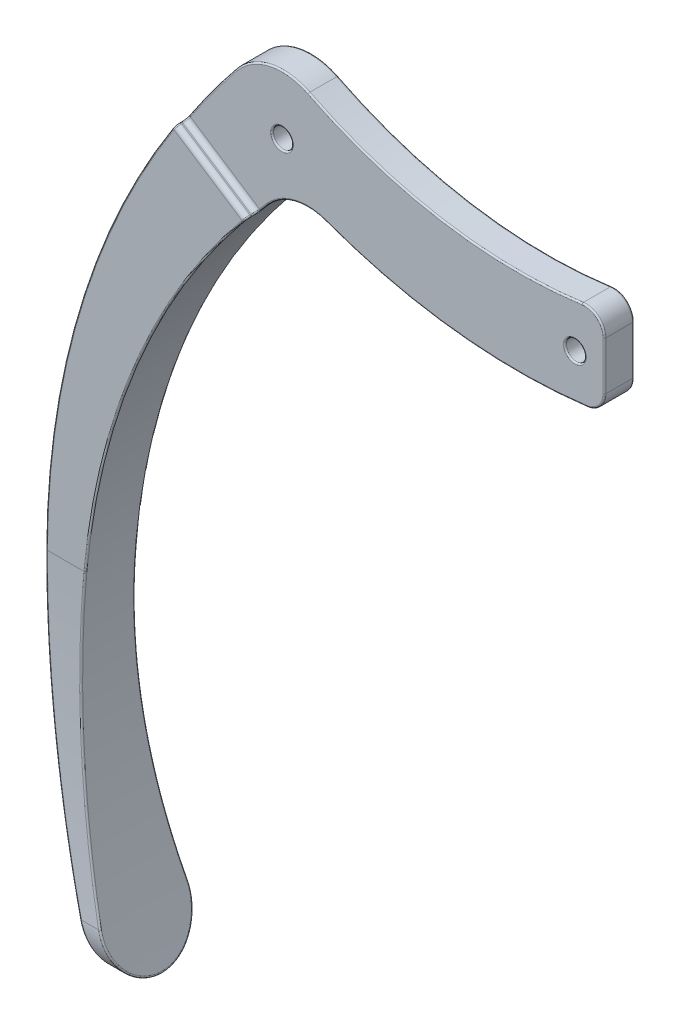
SolidWorks part; units mm, degrees
ref_plane "Front Plane" through (0, 0, 0) normal (0, 0, 1) x (1, 0, 0)
ref_plane "Top Plane" through (0, 0, 0) normal (0, 1, 0) x (1, 0, 0)
ref_plane "Right Plane" through (0, 0, 0) normal (1, 0, 0) x (0, 0, -1)
sketch "Sketch1" plane through (0, 0, 0) normal (0, 0, 1) x (1, 0, 0)
  line L0 (0, -4.5) -> (0, 4.5)
  line L1 (-47.88, -77.96) -> (-46.08, -77.96)
  arc A0 (0, 4.5) -> (-30, 8.7233) centre (-8.7418, 51.0666) cw
  arc A1 (0, -4.5) -> (-28.25, -1.6923) centre (-8.7418, 51.0666) cw
  arc A2 (-28.25, -1.6923) -> (-34.1239, -3.1783) centre (-30.1054, -6.7102) ccw
  arc A3 (-34.1239, -3.1783) -> (-46.08, -77.96) centre (19.2047, -50.0511) ccw
  arc A4 (-30, 8.7233) -> (-37.3384, 7.1573) centre (-32.692, 3.3611) ccw
  arc A5 (-37.3384, 7.1573) -> (-47.88, -77.96) centre (25.0008, -43.7747) ccw
  circle A6 centre (-32.692, 3.3611) radius 1
  arc A7 (0, 0) -> (-26.9332, 2.5558) centre (-8.7418, 51.0666) cw construction
  circle A8 centre (-3, -0.4237) radius 1
  point P4 (0, 0)
  dimension "D2" = 47.38
  dimension "D3" = 56.25
  dimension "D6" = 5.35
  dimension "D7" = 71
  dimension "D9" = 6
  dimension "D10" = 80.5
  dimension "D13" = 2
  dimension "D1" = 9
  dimension "D4" = 30
  dimension "D5" = 28.25
  dimension "D8" = 77.96
  dimension "D11" = 47.88
  dimension "D12" = 1.8
  dimension "D14" = 3
sketch "Sketch3" plane through (0, 0, 0) normal (0, 0, 1) x (1, 0, 0)
  line L0 (0, -33.9364) -> (0, 0) construction
  line L1 (0, -33.9364) -> (-35.1844, -4.4132) construction
  line L2 (0, -4.5) -> (0, 4.5)
  line L3 (-47.88, -77.96) -> (-46.08, -77.96)
  line L5 (-47.88, -77.96) -> (-46.08, -77.96)
  line L6 (-35.1844, -4.4132) -> (-42.3703, 0.2864)
  arc A6 (-30, 8.7233) -> (0, 4.5) centre (-8.7418, 51.0666) ccw
  arc A7 (-30, 8.7233) -> (-37.3384, 7.1573) centre (-32.692, 3.3611) ccw
  arc A8 (-37.3384, 7.1573) -> (-47.88, -77.96) centre (25.0008, -43.7747) ccw
  arc A9 (-34.1239, -3.1783) -> (-46.08, -77.96) centre (19.2047, -50.0511) ccw
  arc A10 (-28.25, -1.6923) -> (-34.1239, -3.1783) centre (-30.1054, -6.7102) ccw
  arc A11 (-28.25, -1.6923) -> (0, -4.5) centre (-8.7418, 51.0666) ccw
  arc A14 (-42.3703, 0.2864) -> (-47.88, -77.96) centre (25.0008, -43.7747) ccw
  arc A15 (-35.1844, -4.4132) -> (-46.08, -77.96) centre (19.2047, -50.0511) ccw
  dimension "D2" = 50
  dimension "D1" = 0
extrude "Boss-Extrude1" add sketch "Sketch3" along normal mid plane 10
sketch "Sketch4" plane through (0, 0, 0) normal (1, 0, 0) x (0, 0, -1)
  line L0 (2.625, 4.9864) -> (-2.625, 4.9864) construction
  line L1 (-2.625, 4.9864) -> (-2.625, -43.5398)
  line L2 (2.625, 4.9864) -> (2.625, -43.5136)
  line L3 (-5, 0.2864) -> (5, 0.2864) construction
  line L4 (2.625, 4.9864) -> (37.248, 4.9864)
  line L5 (37.248, 4.9864) -> (37.248, -91.6112)
  line L6 (37.248, -91.6112) -> (-28.9304, -91.6112)
  line L7 (-28.9304, -91.6112) -> (-28.9304, 4.9864)
  line L8 (-28.9304, 4.9864) -> (-2.625, 4.9864)
  arc A0 (2.625, -43.5136) -> (4.4638, -72.4439) centre (231.1292, -43.5136) ccw
  arc A1 (4.4638, -72.4439) -> (-4.4637, -72.4434) centre (0, -73.0136) cw
  arc A2 (-4.4637, -72.4434) -> (-2.625, -43.5398) centre (-230.7167, -43.5398) ccw
  point P10 (0, 4.9864)
  dimension "D2" = 4.5
  dimension "D1" = 5.25
  dimension "D3" = 78
  dimension "D4" = 29.5
  dimension "D5" = 4.7
extrude "Cut-Extrude2" cut sketch "Sketch4" against normal through all and the other way through all
sketch "Sketch7" plane through (0, 0, 0) normal (0, 0, 1) x (1, 0, 0)
  line L0 (-42.3703, 0.2864) -> (-35.1844, -4.4132) construction
  line L1 (-42.3703, 0.2864) -> (-35.1844, -4.4132)
  line L2 (0, -4.5) -> (0, 4.5)
  line L3 (-47.88, -77.96) -> (-46.08, -77.96)
  line L4 (0, -4.5) -> (0, 4.5)
  circle A1 centre (-3, -0.4237) radius 1
  circle A2 centre (-3, -0.4237) radius 1
  circle A3 centre (-32.692, 3.3611) radius 1
  circle A4 centre (-32.692, 3.3611) radius 1
  arc A6 (-30, 8.7233) -> (0, 4.5) centre (-8.7418, 51.0666) ccw
  arc A7 (-30, 8.7233) -> (-37.3384, 7.1573) centre (-32.692, 3.3611) ccw
  arc A8 (-37.3384, 7.1573) -> (-47.88, -77.96) centre (25.0008, -43.7747) ccw
  arc A9 (-34.1239, -3.1783) -> (-46.08, -77.96) centre (19.2047, -50.0511) ccw
  arc A10 (-28.25, -1.6923) -> (-34.1239, -3.1783) centre (-30.1054, -6.7102) ccw
  arc A11 (-28.25, -1.6923) -> (0, -4.5) centre (-8.7418, 51.0666) ccw
  arc A12 (-30, 8.7233) -> (0, 4.5) centre (-8.7418, 51.0666) ccw
  arc A13 (-30, 8.7233) -> (-37.3384, 7.1573) centre (-32.692, 3.3611) ccw
  arc A14 (-37.3384, 7.1573) -> (-42.3703, 0.2864) centre (25.0008, -43.7747) ccw
  arc A15 (-34.1239, -3.1783) -> (-35.1844, -4.4132) centre (19.2047, -50.0511) ccw
  arc A16 (-28.25, -1.6923) -> (-34.1239, -3.1783) centre (-30.1054, -6.7102) ccw
  arc A17 (-28.25, -1.6923) -> (0, -4.5) centre (-8.7418, 51.0666) ccw
  dimension "D1" = 0
  dimension "D2" = 0
  dimension "D3" = 0
extrude "Boss-Extrude3" add sketch "Sketch7" along normal mid plane 3
fillet "Fillet2" radius 2 2 edges at (0, -4.5, 0) (0, 4.5, 0)
fillet "Fillet3" radius 0.5 4 edges at (-38.7774, -2.0634, -2.625) (-38.7774, -2.0634, -1.5) (-38.7774, -2.0634, 1.5) (-38.7774, -2.0634, 2.625)
fillet "Fillet4" radius 0.15 44 edges at (-35.0639, -4.2699, 1.611) (-35.1844, -4.4132, 2.0625) (-35.2545, -4.4967, 2.4357) (-46.4249, -22.9632, 2.625) (-49.8766, -66.4455, 3.778) (-46.2721, -77.5064, -0.2544) (-51.7949, -49.8025, -2.7116) (-46.4199, -22.951, -2.625) (-35.3047, -4.5569, -2.5142) (-35.1844, -4.4132, -2.0625) (-35.1143, -4.3297, -1.6893) (-42.2674, 0.4433, -1.6096) (-42.3703, 0.2864, -2.0625) (-42.4302, 0.1947, -2.4373) (-52.1812, -20.9014, -2.625) (-48.0933, -77.5015, 0.3293) (-52.1849, -20.914, 2.625) (-42.4728, 0.1292, 2.5154) (-42.3703, 0.2864, 2.0625) (-42.3103, 0.3781, 1.6877) (-31.692, 3.3611, -1.5) (-31.692, 3.3611, 1.5) (-2, -0.4237, -1.5) (-2, -0.4237, 1.5) (-15.1844, -4.8133, -1.5) (0, -0.307, -1.5) (-16.4849, 4.3236, -1.5) (-33.9442, 9.229, -1.5) (-39.7973, 3.9899, -1.5) (-34.4932, -3.6019, -1.5) (-31.4176, -1.5236, -1.5) (-15.1844, -4.8133, 1.5) (0, -0.307, 1.5) (-33.9442, 9.229, 1.5) (-39.7973, 3.9899, 1.5) (-34.4932, -3.6019, 1.5) (-31.4176, -1.5236, 1.5) (-0.6859, 3.6566, -1.5) (-0.5005, -4.0863, -1.5) (-0.6859, 3.6566, 1.5) (-0.5005, -4.0863, 1.5) (-16.4849, 4.3236, 1.5)
